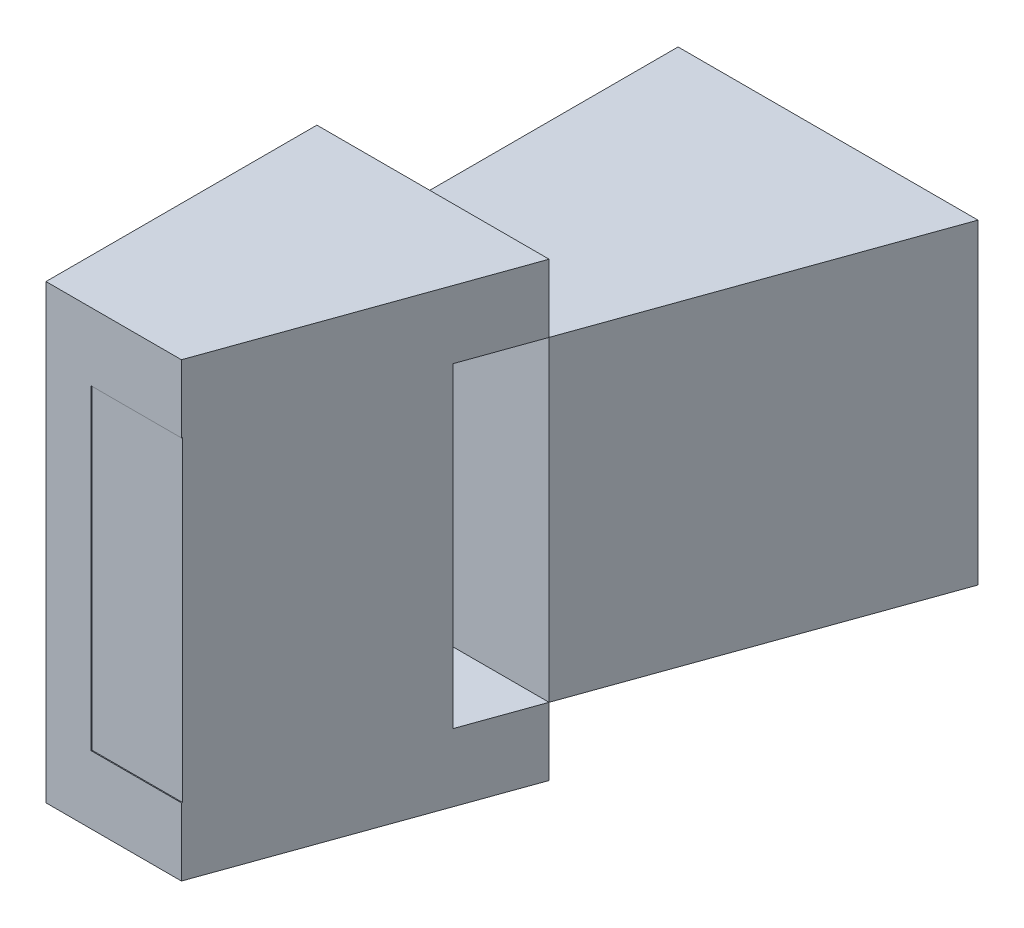
SolidWorks part; units mm, degrees
ref_plane "Plano frontal" through (0, 0, 0) normal (0, 0, 1) x (1, 0, 0)
ref_plane "Plano superior" through (0, 0, 0) normal (0, 1, 0) x (1, 0, 0)
ref_plane "Plano direito" through (0, 0, 0) normal (1, 0, 0) x (0, 0, -1)
sketch "Esboço1" plane through (0, 0, 0) normal (1, 0, 0) x (0, 0, -1)
  line L1 (-41.6099, 28.9783) -> (18.3901, 28.9783)
  line L2 (-41.6099, 28.9783) -> (-41.6099, -71.0217)
  line L3 (-41.6099, -71.0217) -> (18.3901, -71.0217)
  line L4 (18.3901, 28.9783) -> (18.3901, -71.0217)
  dimension "D1" = 60
  dimension "D2" = 100
extrude "Ressalto-extrusão1" add sketch "Esboço1" along normal blind 10
sketch "Esboço2" plane through (10, 0, 0) normal (1, 0, 0) x (0, 0, -1)
  line L0 (18.3901, -71.0217) -> (18.3901, 28.9783) construction
  line L1 (-41.6099, 28.9783) -> (18.3901, 28.9783)
  line L2 (-41.6099, 28.9783) -> (-41.6099, 13.9783)
  line L3 (-41.6099, 13.9783) -> (18.3901, 13.9783)
  line L4 (18.3901, 28.9783) -> (18.3901, 13.9783)
  line L6 (-41.6099, -71.0217) -> (18.3901, -71.0217)
  line L7 (-41.6099, -71.0217) -> (-41.6099, -56.0217)
  line L8 (-41.6099, -56.0217) -> (18.3901, -56.0217)
  line L9 (18.3901, -71.0217) -> (18.3901, -56.0217)
  dimension "D1" = 15
  dimension "D2" = 15
extrude "Ressalto-extrusão2" add sketch "Esboço2" along normal blind 70 separate body
sketch "Esboço3" plane through (0, -71.0217, 0) normal (0, -1, 0) x (1, 0, 0)
  line L0 (30, 41.6099) -> (80, 41.6099)
  line L2 (80, 41.6099) -> (80, -98.3901)
  line L5 (30, 41.6099) -> (80, -98.3901)
extrude "Corte-extrusão3" cut sketch "Esboço3" against normal blind 121 contours L5 L2 L0
sketch "Esboço7" plane through (0, 13.9783, 0) normal (0, -1, 0) x (1, 0, 0)
  line L0 (10, 41.6099) -> (10, -18.3901) construction
  line L1 (10, 41.4079) -> (30.0721, 41.4079)
  line L2 (10, 41.4079) -> (10, -2.7171)
  line L3 (10, -2.7171) -> (40, -2.7171)
  line L5 (30, 41.6099) -> (45.8311, -2.7171)
  line L6 (51.4286, -18.3901) -> (30, 41.6099) construction
  line L7 (40, -2.7171) -> (45.8311, -2.7171)
  line L8 (45.8311, -2.7171) -> (45.6088, -2.8409)
  line M3 (51.4286, -18.3901) -> (30, 41.6099)
  line M5 (10, 41.6099) -> (10, -18.3901)
extrude "Ressalto-extrusão4" add sketch "Esboço7" along normal up to surface (70 mm away) contours L3 L7 L1 M3 M5 up to face at (25.3571, -56.0217, 11.6099)
sketch "Esboço9" plane through (0, 13.9783, 0) normal (0, -1, 0) x (1, 0, 0)
  line L0 (51.4286, -18.3901) -> (76.4286, -88.3901)
  line L1 (10, -18.3901) -> (51.4286, -18.3901)
  line L2 (10, -18.3901) -> (10, -88.3901)
  line L3 (10, -88.3901) -> (76.4286, -88.3901)
extrude "Ressalto-extrusão5" add sketch "Esboço9" along normal up to surface (70 mm away) up to face at (29.3149, -56.0217, -10.5536)
